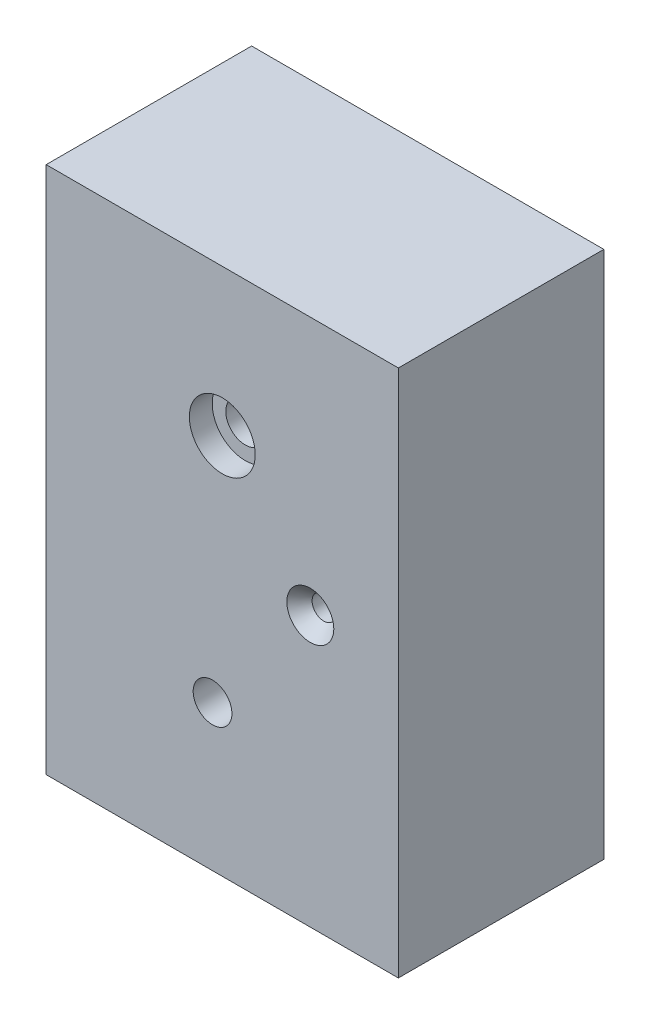
SolidWorks part; units mm, degrees
ref_plane "Front Plane" through (0, 0, 0) normal (0, 0, 1) x (1, 0, 0)
ref_plane "Top Plane" through (0, 0, 0) normal (0, 1, 0) x (1, 0, 0)
ref_plane "Right Plane" through (0, 0, 0) normal (1, 0, 0) x (0, 0, -1)
sketch "Sketch1" plane through (0, 0, 0) normal (0, 0, 1) x (1, 0, 0)
  line L1 (0, 0) -> (300, 0)
  line L2 (0, 0) -> (0, 450)
  line L3 (0, 450) -> (300, 450)
  line L4 (300, 0) -> (300, 450)
  dimension "D1" = 450
  dimension "D2" = 300
extrude "Boss-Extrude1" add sketch "Sketch1" along normal blind 175
hole_wizard "CBORE for M30 Hex Head Cap Screw1" positions "Sketch5" profile "Sketch6" counterbore size "M30" standard "ANSI Metric"
sketch "Sketch5" plane through (0, 0, 175) normal (0, 0, 1) x (1, 0, 0)
  line L0 (300, 450) -> (0, 450) construction
  line L1 (0, 450) -> (0, 0) construction
  point P0 (150, 325)
  dimension "D1" = 125
  dimension "D2" = 150
sketch "Sketch6" plane through (150, 325, 175) normal (1, 0, 0) x (0, -1, 0)
  line L0 (0, 0) -> (0, 184.9132)
  line L1 (0, 184.9132) -> (16.5, 174.999)
  line L2 (16.5, 174.999) -> (16.5, 19.48)
  line L3 (16.5, 19.48) -> (28.06, 19.48)
  line L4 (28.06, 19.48) -> (28.06, 0)
  line L5 (28.06, 0) -> (0, 0)
  line L10 (0, 184.9132) -> (-16.5, 174.999) construction
  line L11 (0, -6.35) -> (0, 107.95) construction
  dimension "Hole Dia." = 33
  dimension "Hole Depth" = 174.999
  dimension "C'Bore Dia." = 56.12
  dimension "C'Bore Depth" = 19.48
  dimension "Drill Angle" = 118
hole_wizard "M36x3.0 Tapped Hole1" positions "Sketch7" profile "Sketch8" tap size "M36x3.0" standard "ANSI Metric" end condition through all
sketch "Sketch7" plane through (0, 0, 175) normal (0, 0, 1) x (1, 0, 0)
  point P0 (141.6982, 124.1233)
sketch "Sketch8" plane through (141.6982, 124.1233, 175) normal (1, 0, 0) x (0, -1, 0)
  line L0 (0, 0) -> (0, 175)
  line L1 (0, 175) -> (16.5, 175)
  line L2 (16.5, 175) -> (16.5, 0)
  line L5 (16.5, 0) -> (0, 0)
  line L11 (0, -6.35) -> (0, 107.95) construction
  dimension "Thru Tap Drill Dia." = 33
  dimension "Thru Tap Drill Depth" = 175
cosmetic thread "Hole Thread1" parameters "D2"=36
hole_wizard "Hole1" positions "Sketch9" profile "Sketch10" legacy
sketch "Sketch9" plane through (0, 0, 175) normal (0, 0, 1) x (1, 0, 0)
  line L0 (300, 0) -> (300, 450) construction
  line L1 (300, 450) -> (0, 450) construction
  point P0 (225, 230)
  dimension "D1" = 75
  dimension "D2" = 220
sketch "Sketch10" plane through (225, 230, 175) normal (1, 0, 0) x (0, -1, 0)
  line L0 (0, 0) -> (0, 174.999)
  line L1 (0, 174.999) -> (10, 174.999)
  line L2 (10, 174.999) -> (10, 11.5037)
  line L3 (10, 11.5037) -> (20, 0)
  line L4 (20, 0) -> (0, 0)
  line L5 (0, -6.4453) -> (0, 115.525) construction
  line L6 (-10, 11.5037) -> (-20, 0) construction
  dimension "Diameter" = 20
  dimension "Depth" = 174.999
  dimension "C-Sink Angle" = 82
  dimension "C-Sink Diameter" = 40
